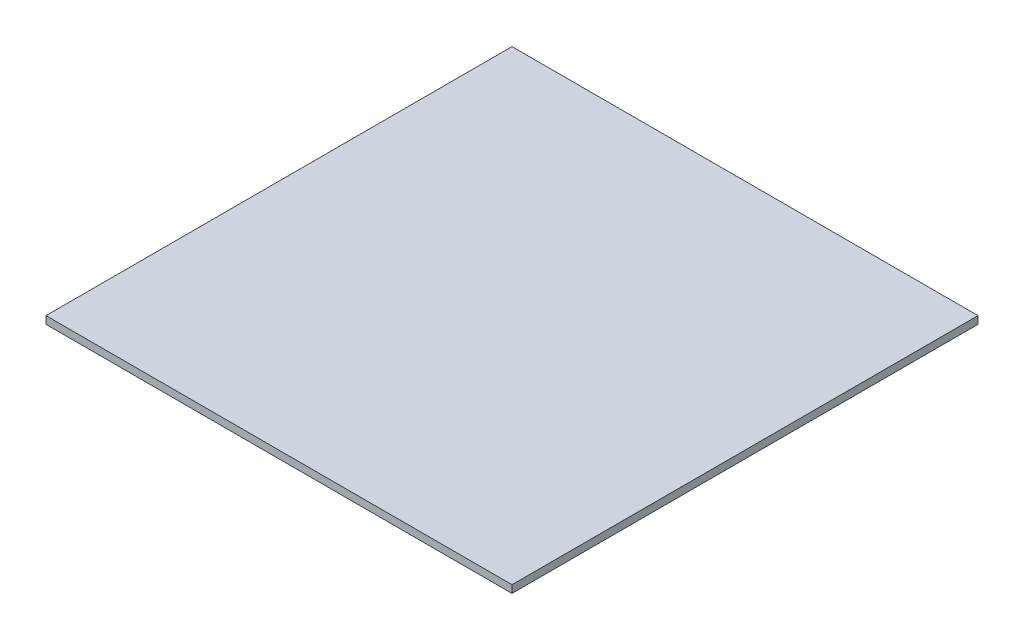
SolidWorks part; units mm, degrees
material "6061 Alloy"
ref_plane "Front Plane" through (0, 0, 0) normal (0, 0, 1) x (1, 0, 0)
ref_plane "Top Plane" through (0, 0, 0) normal (0, 1, 0) x (1, 0, 0)
ref_plane "Right Plane" through (0, 0, 0) normal (1, 0, 0) x (0, 0, -1)
sketch "Sketch1" plane through (0, 0, 0) normal (0, 1, 0) x (1, 0, 0)
  line L1 (-50, 50) -> (50, 50)
  line L2 (-50, 50) -> (-50, -50)
  line L3 (-50, -50) -> (50, -50)
  line L4 (50, 50) -> (50, -50)
  line L5 (-50, 50) -> (50, -50) construction
  line L6 (-50, -50) -> (50, 50) construction
  point P0 (0, 0)
  dimension "D1" = 100
  dimension "D2" = 100
extrude "Boss-Extrude1" add sketch "Sketch1" along normal blind 1.6256
